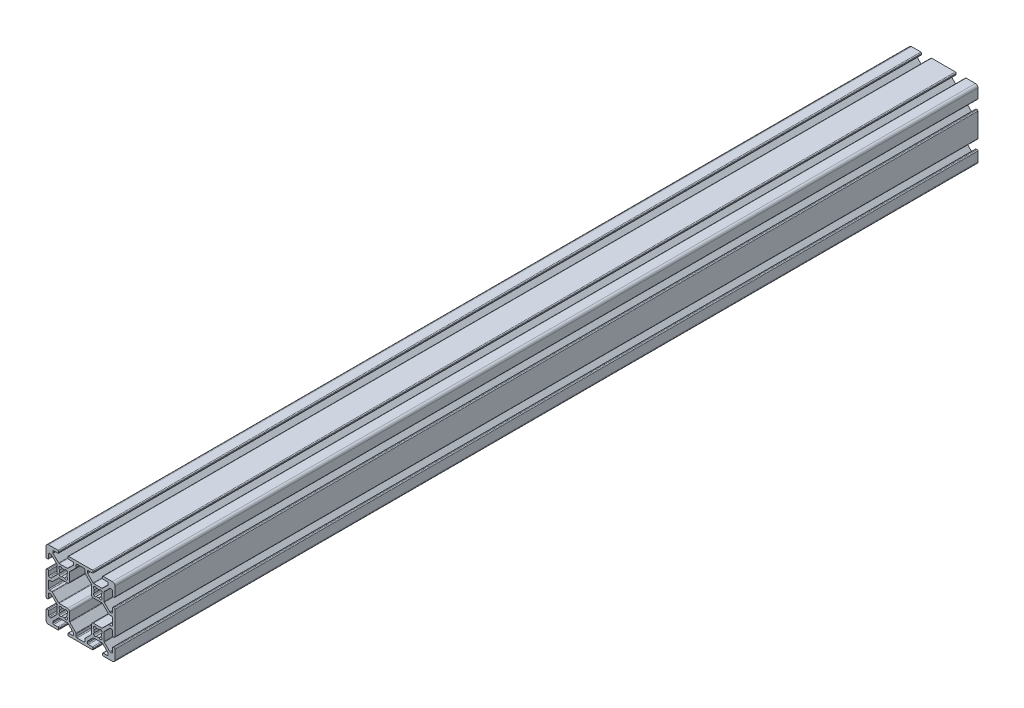
SolidWorks part; units mm, degrees
material "6105-T5 Aluminum"
ref_plane "Front Plane" through (0, 0, 0) normal (0, 0, 1) x (1, 0, 0)
ref_plane "Top Plane" through (0, 0, 0) normal (0, 1, 0) x (1, 0, 0)
ref_plane "Right Plane" through (0, 0, 0) normal (1, 0, 0) x (0, 0, -1)
sketch "Sketch1" plane through (0, 0, 0) normal (0, 0, 1) x (1, 0, 0)
  line L0 (-2.1249, 17.6955) -> (-2.3045, 17.8751)
  line L1 (-2.3045, 22.1249) -> (-2.1249, 22.3045)
  line L2 (2.1249, 22.3045) -> (2.3045, 22.1249)
  line L3 (2.3045, 17.8751) -> (2.1249, 17.6955)
  line L4 (-22.1249, 17.6955) -> (-22.3045, 17.8751)
  line L5 (-22.3045, 22.1249) -> (-22.1249, 22.3045)
  line L6 (-17.8751, 22.3045) -> (-17.6955, 22.1249)
  line L7 (-17.6955, 17.8751) -> (-17.8751, 17.6955)
  line L8 (-2.1249, -2.3045) -> (-2.3045, -2.1249)
  line L9 (-2.3045, 2.1249) -> (-2.1249, 2.3045)
  line L10 (2.1249, 2.3045) -> (2.3045, 2.1249)
  line L11 (2.3045, -2.1249) -> (2.1249, -2.3045)
  line L12 (-12.505, -7.992) -> (-12.505, -6.6448)
  line L13 (-12.6538, -6.2856) -> (-16.1962, -2.7431)
  line L14 (-16.345, -2.3839) -> (-16.345, 2.512)
  line L15 (-17.488, 3.655) -> (-22.3839, 3.655)
  line L16 (-22.7431, 3.8038) -> (-26.2856, 7.3462)
  line L17 (-26.6448, 7.495) -> (-27.992, 7.495)
  line L18 (-28.5, 8.003) -> (-28.5, 11.997)
  line L19 (-27.992, 12.505) -> (-26.6448, 12.505)
  line L20 (-26.2856, 12.6538) -> (-22.7431, 16.1962)
  line L21 (-22.3839, 16.345) -> (-17.488, 16.345)
  line L22 (-16.345, 17.488) -> (-16.345, 22.3839)
  line L23 (-16.1962, 22.7431) -> (-12.6538, 26.2856)
  line L24 (-12.505, 26.6448) -> (-12.505, 27.992)
  line L25 (-11.997, 28.5) -> (-8.003, 28.5)
  line L26 (-7.495, 27.992) -> (-7.495, 26.6448)
  line L27 (-7.3462, 26.2856) -> (-3.8038, 22.7431)
  line L28 (-3.655, 22.3839) -> (-3.655, 17.488)
  line L29 (-2.512, 16.345) -> (2.3839, 16.345)
  line L30 (2.7431, 16.1962) -> (6.2856, 12.6538)
  line L31 (6.6448, 12.505) -> (7.992, 12.505)
  line L32 (8.5, 11.997) -> (8.5, 8.003)
  line L33 (7.992, 7.495) -> (6.6448, 7.495)
  line L34 (6.2856, 7.3462) -> (2.7431, 3.8038)
  line L35 (2.3839, 3.655) -> (-2.512, 3.655)
  line L36 (-3.655, 2.512) -> (-3.655, -2.3839)
  line L37 (-3.8038, -2.7431) -> (-7.3462, -6.2856)
  line L38 (-7.495, -6.6448) -> (-7.495, -7.992)
  line L39 (-8.003, -8.5) -> (-11.997, -8.5)
  line L40 (-22.1249, -2.3045) -> (-22.3045, -2.1249)
  line L41 (-22.3045, 2.1249) -> (-22.1249, 2.3045)
  line L42 (-17.8751, 2.3045) -> (-17.6955, 2.1249)
  line L43 (-17.6955, -2.1249) -> (-17.8751, -2.3045)
  line L44 (-22.3839, -3.655) -> (-17.6161, -3.655)
  line L45 (-17.2569, -3.8038) -> (-14.1538, -6.9069)
  line L46 (-14.005, -7.2661) -> (-14.005, -7.992)
  line L47 (-14.513, -8.5) -> (-16.862, -8.5)
  line L48 (-17.37, -9.008) -> (-17.37, -9.492)
  line L49 (-16.862, -10) -> (-3.138, -10)
  line L50 (-2.63, -9.492) -> (-2.63, -9.008)
  line L51 (-3.138, -8.5) -> (-5.487, -8.5)
  line L52 (-5.995, -7.992) -> (-5.995, -7.2661)
  line L53 (-5.8462, -6.9069) -> (-2.7431, -3.8038)
  line L54 (-2.3839, -3.655) -> (2.3839, -3.655)
  line L55 (2.7431, -3.8038) -> (5.8462, -6.9069)
  line L56 (5.995, -7.2661) -> (5.995, -7.992)
  line L57 (5.487, -8.5) -> (3.138, -8.5)
  line L58 (2.63, -9.008) -> (2.63, -9.492)
  line L59 (3.138, -10) -> (8.5, -10)
  line L60 (10, -8.5) -> (10, -3.138)
  line L61 (9.492, -2.63) -> (9.008, -2.63)
  line L62 (8.5, -3.138) -> (8.5, -5.487)
  line L63 (7.992, -5.995) -> (7.2661, -5.995)
  line L64 (6.9069, -5.8462) -> (3.8038, -2.7431)
  line L65 (3.655, -2.3839) -> (3.655, 2.3839)
  line L66 (3.8038, 2.7431) -> (6.9069, 5.8462)
  line L67 (7.2661, 5.995) -> (7.992, 5.995)
  line L68 (8.5, 5.487) -> (8.5, 3.138)
  line L69 (9.008, 2.63) -> (9.492, 2.63)
  line L70 (10, 3.138) -> (10, 16.862)
  line L71 (9.492, 17.37) -> (9.008, 17.37)
  line L72 (8.5, 16.862) -> (8.5, 14.513)
  line L73 (7.992, 14.005) -> (7.2661, 14.005)
  line L74 (6.9069, 14.1538) -> (3.8038, 17.2569)
  line L75 (3.655, 17.6161) -> (3.655, 22.3839)
  line L76 (3.8038, 22.7431) -> (6.9069, 25.8462)
  line L77 (7.2661, 25.995) -> (7.992, 25.995)
  line L78 (8.5, 25.487) -> (8.5, 23.138)
  line L79 (9.008, 22.63) -> (9.492, 22.63)
  line L80 (10, 23.138) -> (10, 28.5)
  line L81 (8.5, 30) -> (3.138, 30)
  line L82 (2.63, 29.492) -> (2.63, 29.008)
  line L83 (3.138, 28.5) -> (5.487, 28.5)
  line L84 (5.995, 27.992) -> (5.995, 27.2661)
  line L85 (5.8462, 26.9069) -> (2.7431, 23.8038)
  line L86 (2.3839, 23.655) -> (-2.3839, 23.655)
  line L87 (-2.7431, 23.8038) -> (-5.8462, 26.9069)
  line L88 (-5.995, 27.2661) -> (-5.995, 27.992)
  line L89 (-5.487, 28.5) -> (-3.138, 28.5)
  line L90 (-2.63, 29.008) -> (-2.63, 29.492)
  line L91 (-3.138, 30) -> (-16.862, 30)
  line L92 (-17.37, 29.492) -> (-17.37, 29.008)
  line L93 (-16.862, 28.5) -> (-14.513, 28.5)
  line L94 (-14.005, 27.992) -> (-14.005, 27.2661)
  line L95 (-14.1538, 26.9069) -> (-17.2569, 23.8038)
  line L96 (-17.6161, 23.655) -> (-22.3839, 23.655)
  line L97 (-22.7431, 23.8038) -> (-25.8462, 26.9069)
  line L98 (-25.995, 27.2661) -> (-25.995, 27.992)
  line L99 (-25.487, 28.5) -> (-23.138, 28.5)
  line L100 (-22.63, 29.008) -> (-22.63, 29.492)
  line L101 (-23.138, 30) -> (-28.5, 30)
  line L102 (-30, 28.5) -> (-30, 23.138)
  line L103 (-29.492, 22.63) -> (-29.008, 22.63)
  line L104 (-28.5, 23.138) -> (-28.5, 25.487)
  line L105 (-27.992, 25.995) -> (-27.2661, 25.995)
  line L106 (-26.9069, 25.8462) -> (-23.8038, 22.7431)
  line L107 (-23.655, 22.3839) -> (-23.655, 17.6161)
  line L108 (-23.8038, 17.2569) -> (-26.9069, 14.1538)
  line L109 (-27.2661, 14.005) -> (-27.992, 14.005)
  line L110 (-28.5, 14.513) -> (-28.5, 16.862)
  line L111 (-29.008, 17.37) -> (-29.492, 17.37)
  line L112 (-30, 16.862) -> (-30, 3.138)
  line L113 (-29.492, 2.63) -> (-29.008, 2.63)
  line L114 (-28.5, 3.138) -> (-28.5, 5.487)
  line L115 (-27.992, 5.995) -> (-27.2661, 5.995)
  line L116 (-26.9069, 5.8462) -> (-23.8038, 2.7431)
  line L117 (-23.655, 2.3839) -> (-23.655, -2.3839)
  line L118 (-23.8038, -2.7431) -> (-26.9069, -5.8462)
  line L119 (-27.2661, -5.995) -> (-27.992, -5.995)
  line L120 (-28.5, -5.487) -> (-28.5, -3.138)
  line L121 (-29.008, -2.63) -> (-29.492, -2.63)
  line L122 (-30, -3.138) -> (-30, -8.5)
  line L123 (-28.5, -10) -> (-23.138, -10)
  line L124 (-22.63, -9.492) -> (-22.63, -9.008)
  line L125 (-23.138, -8.5) -> (-25.487, -8.5)
  line L126 (-25.995, -7.992) -> (-25.995, -7.2661)
  line L127 (-25.8462, -6.9069) -> (-22.7431, -3.8038)
  arc A0 (-1.9351, 19.196) -> (-2.3045, 17.8751) centre (-1.748, 18.4316) ccw
  arc A1 (-1.9351, 20.804) -> (-1.9351, 19.196) centre (0, 20) ccw
  arc A2 (-2.3045, 22.1249) -> (-1.9351, 20.804) centre (-1.748, 21.5684) ccw
  arc A3 (-0.804, 21.9351) -> (-2.1249, 22.3045) centre (-1.5684, 21.748) ccw
  arc A4 (0.804, 21.9351) -> (-0.804, 21.9351) centre (0, 20) ccw
  arc A5 (2.1249, 22.3045) -> (0.804, 21.9351) centre (1.5684, 21.748) ccw
  arc A6 (1.9351, 20.804) -> (2.3045, 22.1249) centre (1.748, 21.5684) ccw
  arc A7 (1.9351, 19.196) -> (1.9351, 20.804) centre (0, 20) ccw
  arc A8 (2.3045, 17.8751) -> (1.9351, 19.196) centre (1.748, 18.4316) ccw
  arc A9 (0.804, 18.0649) -> (2.1249, 17.6955) centre (1.5684, 18.252) ccw
  arc A10 (-0.804, 18.0649) -> (0.804, 18.0649) centre (0, 20) ccw
  arc A11 (-2.1249, 17.6955) -> (-0.804, 18.0649) centre (-1.5684, 18.252) ccw
  arc A12 (-21.9351, 19.196) -> (-22.3045, 17.8751) centre (-21.748, 18.4316) ccw
  arc A13 (-21.9351, 20.804) -> (-21.9351, 19.196) centre (-20, 20) ccw
  arc A14 (-22.3045, 22.1249) -> (-21.9351, 20.804) centre (-21.748, 21.5684) ccw
  arc A15 (-20.804, 21.9351) -> (-22.1249, 22.3045) centre (-21.5684, 21.748) ccw
  arc A16 (-19.196, 21.9351) -> (-20.804, 21.9351) centre (-20, 20) ccw
  arc A17 (-17.8751, 22.3045) -> (-19.196, 21.9351) centre (-18.4316, 21.748) ccw
  arc A18 (-18.0649, 20.804) -> (-17.6955, 22.1249) centre (-18.252, 21.5684) ccw
  arc A19 (-18.0649, 19.196) -> (-18.0649, 20.804) centre (-20, 20) ccw
  arc A20 (-17.6955, 17.8751) -> (-18.0649, 19.196) centre (-18.252, 18.4316) ccw
  arc A21 (-19.196, 18.0649) -> (-17.8751, 17.6955) centre (-18.4316, 18.252) ccw
  arc A22 (-20.804, 18.0649) -> (-19.196, 18.0649) centre (-20, 20) ccw
  arc A23 (-22.1249, 17.6955) -> (-20.804, 18.0649) centre (-21.5684, 18.252) ccw
  arc A24 (-1.9351, -0.804) -> (-2.3045, -2.1249) centre (-1.748, -1.5684) ccw
  arc A25 (-1.9351, 0.804) -> (-1.9351, -0.804) centre (0, 0) ccw
  arc A26 (-2.3045, 2.1249) -> (-1.9351, 0.804) centre (-1.748, 1.5684) ccw
  arc A27 (-0.804, 1.9351) -> (-2.1249, 2.3045) centre (-1.5684, 1.748) ccw
  arc A28 (0.804, 1.9351) -> (-0.804, 1.9351) centre (0, 0) ccw
  arc A29 (2.1249, 2.3045) -> (0.804, 1.9351) centre (1.5684, 1.748) ccw
  arc A30 (1.9351, 0.804) -> (2.3045, 2.1249) centre (1.748, 1.5684) ccw
  arc A31 (1.9351, -0.804) -> (1.9351, 0.804) centre (0, 0) ccw
  arc A32 (2.3045, -2.1249) -> (1.9351, -0.804) centre (1.748, -1.5684) ccw
  arc A33 (0.804, -1.9351) -> (2.1249, -2.3045) centre (1.5684, -1.748) ccw
  arc A34 (-0.804, -1.9351) -> (0.804, -1.9351) centre (0, 0) ccw
  arc A35 (-2.1249, -2.3045) -> (-0.804, -1.9351) centre (-1.5684, -1.748) ccw
  arc A36 (-12.505, -7.992) -> (-11.997, -8.5) centre (-11.997, -7.992) ccw
  arc A37 (-12.505, -6.6448) -> (-12.6538, -6.2856) centre (-13.013, -6.6448) ccw
  arc A38 (-16.345, -2.3839) -> (-16.1962, -2.7431) centre (-15.837, -2.3839) ccw
  arc A39 (-16.345, 2.512) -> (-17.488, 3.655) centre (-17.488, 2.512) ccw
  arc A40 (-22.7431, 3.8038) -> (-22.3839, 3.655) centre (-22.3839, 4.163) ccw
  arc A41 (-26.2856, 7.3462) -> (-26.6448, 7.495) centre (-26.6448, 6.987) ccw
  arc A42 (-28.5, 8.003) -> (-27.992, 7.495) centre (-27.992, 8.003) ccw
  arc A43 (-27.992, 12.505) -> (-28.5, 11.997) centre (-27.992, 11.997) ccw
  arc A44 (-26.6448, 12.505) -> (-26.2856, 12.6538) centre (-26.6448, 13.013) ccw
  arc A45 (-22.3839, 16.345) -> (-22.7431, 16.1962) centre (-22.3839, 15.837) ccw
  arc A46 (-17.488, 16.345) -> (-16.345, 17.488) centre (-17.488, 17.488) ccw
  arc A47 (-16.1962, 22.7431) -> (-16.345, 22.3839) centre (-15.837, 22.3839) ccw
  arc A48 (-12.6538, 26.2856) -> (-12.505, 26.6448) centre (-13.013, 26.6448) ccw
  arc A49 (-11.997, 28.5) -> (-12.505, 27.992) centre (-11.997, 27.992) ccw
  arc A50 (-7.495, 27.992) -> (-8.003, 28.5) centre (-8.003, 27.992) ccw
  arc A51 (-7.495, 26.6448) -> (-7.3462, 26.2856) centre (-6.987, 26.6448) ccw
  arc A52 (-3.655, 22.3839) -> (-3.8038, 22.7431) centre (-4.163, 22.3839) ccw
  arc A53 (-3.655, 17.488) -> (-2.512, 16.345) centre (-2.512, 17.488) ccw
  arc A54 (2.7431, 16.1962) -> (2.3839, 16.345) centre (2.3839, 15.837) ccw
  arc A55 (6.2856, 12.6538) -> (6.6448, 12.505) centre (6.6448, 13.013) ccw
  arc A56 (8.5, 11.997) -> (7.992, 12.505) centre (7.992, 11.997) ccw
  arc A57 (7.992, 7.495) -> (8.5, 8.003) centre (7.992, 8.003) ccw
  arc A58 (6.6448, 7.495) -> (6.2856, 7.3462) centre (6.6448, 6.987) ccw
  arc A59 (2.3839, 3.655) -> (2.7431, 3.8038) centre (2.3839, 4.163) ccw
  arc A60 (-2.512, 3.655) -> (-3.655, 2.512) centre (-2.512, 2.512) ccw
  arc A61 (-3.8038, -2.7431) -> (-3.655, -2.3839) centre (-4.163, -2.3839) ccw
  arc A62 (-7.3462, -6.2856) -> (-7.495, -6.6448) centre (-6.987, -6.6448) ccw
  arc A63 (-8.003, -8.5) -> (-7.495, -7.992) centre (-8.003, -7.992) ccw
  arc A64 (-21.9351, -0.804) -> (-22.3045, -2.1249) centre (-21.748, -1.5684) ccw
  arc A65 (-21.9351, 0.804) -> (-21.9351, -0.804) centre (-20, 0) ccw
  arc A66 (-22.3045, 2.1249) -> (-21.9351, 0.804) centre (-21.748, 1.5684) ccw
  arc A67 (-20.804, 1.9351) -> (-22.1249, 2.3045) centre (-21.5684, 1.748) ccw
  arc A68 (-19.196, 1.9351) -> (-20.804, 1.9351) centre (-20, 0) ccw
  arc A69 (-17.8751, 2.3045) -> (-19.196, 1.9351) centre (-18.4316, 1.748) ccw
  arc A70 (-18.0649, 0.804) -> (-17.6955, 2.1249) centre (-18.252, 1.5684) ccw
  arc A71 (-18.0649, -0.804) -> (-18.0649, 0.804) centre (-20, 0) ccw
  arc A72 (-17.6955, -2.1249) -> (-18.0649, -0.804) centre (-18.252, -1.5684) ccw
  arc A73 (-19.196, -1.9351) -> (-17.8751, -2.3045) centre (-18.4316, -1.748) ccw
  arc A74 (-20.804, -1.9351) -> (-19.196, -1.9351) centre (-20, 0) ccw
  arc A75 (-22.1249, -2.3045) -> (-20.804, -1.9351) centre (-21.5684, -1.748) ccw
  arc A76 (-22.3839, -3.655) -> (-22.7431, -3.8038) centre (-22.3839, -4.163) ccw
  arc A77 (-17.2569, -3.8038) -> (-17.6161, -3.655) centre (-17.6161, -4.163) ccw
  arc A78 (-14.005, -7.2661) -> (-14.1538, -6.9069) centre (-14.513, -7.2661) ccw
  arc A79 (-14.513, -8.5) -> (-14.005, -7.992) centre (-14.513, -7.992) ccw
  arc A80 (-16.862, -8.5) -> (-17.37, -9.008) centre (-16.862, -9.008) ccw
  arc A81 (-17.37, -9.492) -> (-16.862, -10) centre (-16.862, -9.492) ccw
  arc A82 (-3.138, -10) -> (-2.63, -9.492) centre (-3.138, -9.492) ccw
  arc A83 (-2.63, -9.008) -> (-3.138, -8.5) centre (-3.138, -9.008) ccw
  arc A84 (-5.995, -7.992) -> (-5.487, -8.5) centre (-5.487, -7.992) ccw
  arc A85 (-5.8462, -6.9069) -> (-5.995, -7.2661) centre (-5.487, -7.2661) ccw
  arc A86 (-2.3839, -3.655) -> (-2.7431, -3.8038) centre (-2.3839, -4.163) ccw
  arc A87 (2.7431, -3.8038) -> (2.3839, -3.655) centre (2.3839, -4.163) ccw
  arc A88 (5.995, -7.2661) -> (5.8462, -6.9069) centre (5.487, -7.2661) ccw
  arc A89 (5.487, -8.5) -> (5.995, -7.992) centre (5.487, -7.992) ccw
  arc A90 (3.138, -8.5) -> (2.63, -9.008) centre (3.138, -9.008) ccw
  arc A91 (2.63, -9.492) -> (3.138, -10) centre (3.138, -9.492) ccw
  arc A92 (8.5, -10) -> (10, -8.5) centre (8.5, -8.5) ccw
  arc A93 (10, -3.138) -> (9.492, -2.63) centre (9.492, -3.138) ccw
  arc A94 (9.008, -2.63) -> (8.5, -3.138) centre (9.008, -3.138) ccw
  arc A95 (7.992, -5.995) -> (8.5, -5.487) centre (7.992, -5.487) ccw
  arc A96 (6.9069, -5.8462) -> (7.2661, -5.995) centre (7.2661, -5.487) ccw
  arc A97 (3.655, -2.3839) -> (3.8038, -2.7431) centre (4.163, -2.3839) ccw
  arc A98 (3.8038, 2.7431) -> (3.655, 2.3839) centre (4.163, 2.3839) ccw
  arc A99 (7.2661, 5.995) -> (6.9069, 5.8462) centre (7.2661, 5.487) ccw
  arc A100 (8.5, 5.487) -> (7.992, 5.995) centre (7.992, 5.487) ccw
  arc A101 (8.5, 3.138) -> (9.008, 2.63) centre (9.008, 3.138) ccw
  arc A102 (9.492, 2.63) -> (10, 3.138) centre (9.492, 3.138) ccw
  arc A103 (10, 16.862) -> (9.492, 17.37) centre (9.492, 16.862) ccw
  arc A104 (9.008, 17.37) -> (8.5, 16.862) centre (9.008, 16.862) ccw
  arc A105 (7.992, 14.005) -> (8.5, 14.513) centre (7.992, 14.513) ccw
  arc A106 (6.9069, 14.1538) -> (7.2661, 14.005) centre (7.2661, 14.513) ccw
  arc A107 (3.655, 17.6161) -> (3.8038, 17.2569) centre (4.163, 17.6161) ccw
  arc A108 (3.8038, 22.7431) -> (3.655, 22.3839) centre (4.163, 22.3839) ccw
  arc A109 (7.2661, 25.995) -> (6.9069, 25.8462) centre (7.2661, 25.487) ccw
  arc A110 (8.5, 25.487) -> (7.992, 25.995) centre (7.992, 25.487) ccw
  arc A111 (8.5, 23.138) -> (9.008, 22.63) centre (9.008, 23.138) ccw
  arc A112 (9.492, 22.63) -> (10, 23.138) centre (9.492, 23.138) ccw
  arc A113 (10, 28.5) -> (8.5, 30) centre (8.5, 28.5) ccw
  arc A114 (3.138, 30) -> (2.63, 29.492) centre (3.138, 29.492) ccw
  arc A115 (2.63, 29.008) -> (3.138, 28.5) centre (3.138, 29.008) ccw
  arc A116 (5.995, 27.992) -> (5.487, 28.5) centre (5.487, 27.992) ccw
  arc A117 (5.8462, 26.9069) -> (5.995, 27.2661) centre (5.487, 27.2661) ccw
  arc A118 (2.3839, 23.655) -> (2.7431, 23.8038) centre (2.3839, 24.163) ccw
  arc A119 (-2.7431, 23.8038) -> (-2.3839, 23.655) centre (-2.3839, 24.163) ccw
  arc A120 (-5.995, 27.2661) -> (-5.8462, 26.9069) centre (-5.487, 27.2661) ccw
  arc A121 (-5.487, 28.5) -> (-5.995, 27.992) centre (-5.487, 27.992) ccw
  arc A122 (-3.138, 28.5) -> (-2.63, 29.008) centre (-3.138, 29.008) ccw
  arc A123 (-2.63, 29.492) -> (-3.138, 30) centre (-3.138, 29.492) ccw
  arc A124 (-16.862, 30) -> (-17.37, 29.492) centre (-16.862, 29.492) ccw
  arc A125 (-17.37, 29.008) -> (-16.862, 28.5) centre (-16.862, 29.008) ccw
  arc A126 (-14.005, 27.992) -> (-14.513, 28.5) centre (-14.513, 27.992) ccw
  arc A127 (-14.1538, 26.9069) -> (-14.005, 27.2661) centre (-14.513, 27.2661) ccw
  arc A128 (-17.6161, 23.655) -> (-17.2569, 23.8038) centre (-17.6161, 24.163) ccw
  arc A129 (-22.7431, 23.8038) -> (-22.3839, 23.655) centre (-22.3839, 24.163) ccw
  arc A130 (-25.995, 27.2661) -> (-25.8462, 26.9069) centre (-25.487, 27.2661) ccw
  arc A131 (-25.487, 28.5) -> (-25.995, 27.992) centre (-25.487, 27.992) ccw
  arc A132 (-23.138, 28.5) -> (-22.63, 29.008) centre (-23.138, 29.008) ccw
  arc A133 (-22.63, 29.492) -> (-23.138, 30) centre (-23.138, 29.492) ccw
  arc A134 (-28.5, 30) -> (-30, 28.5) centre (-28.5, 28.5) ccw
  arc A135 (-30, 23.138) -> (-29.492, 22.63) centre (-29.492, 23.138) ccw
  arc A136 (-29.008, 22.63) -> (-28.5, 23.138) centre (-29.008, 23.138) ccw
  arc A137 (-27.992, 25.995) -> (-28.5, 25.487) centre (-27.992, 25.487) ccw
  arc A138 (-26.9069, 25.8462) -> (-27.2661, 25.995) centre (-27.2661, 25.487) ccw
  arc A139 (-23.655, 22.3839) -> (-23.8038, 22.7431) centre (-24.163, 22.3839) ccw
  arc A140 (-23.8038, 17.2569) -> (-23.655, 17.6161) centre (-24.163, 17.6161) ccw
  arc A141 (-27.2661, 14.005) -> (-26.9069, 14.1538) centre (-27.2661, 14.513) ccw
  arc A142 (-28.5, 14.513) -> (-27.992, 14.005) centre (-27.992, 14.513) ccw
  arc A143 (-28.5, 16.862) -> (-29.008, 17.37) centre (-29.008, 16.862) ccw
  arc A144 (-29.492, 17.37) -> (-30, 16.862) centre (-29.492, 16.862) ccw
  arc A145 (-30, 3.138) -> (-29.492, 2.63) centre (-29.492, 3.138) ccw
  arc A146 (-29.008, 2.63) -> (-28.5, 3.138) centre (-29.008, 3.138) ccw
  arc A147 (-27.992, 5.995) -> (-28.5, 5.487) centre (-27.992, 5.487) ccw
  arc A148 (-26.9069, 5.8462) -> (-27.2661, 5.995) centre (-27.2661, 5.487) ccw
  arc A149 (-23.655, 2.3839) -> (-23.8038, 2.7431) centre (-24.163, 2.3839) ccw
  arc A150 (-23.8038, -2.7431) -> (-23.655, -2.3839) centre (-24.163, -2.3839) ccw
  arc A151 (-27.2661, -5.995) -> (-26.9069, -5.8462) centre (-27.2661, -5.487) ccw
  arc A152 (-28.5, -5.487) -> (-27.992, -5.995) centre (-27.992, -5.487) ccw
  arc A153 (-28.5, -3.138) -> (-29.008, -2.63) centre (-29.008, -3.138) ccw
  arc A154 (-29.492, -2.63) -> (-30, -3.138) centre (-29.492, -3.138) ccw
  arc A155 (-30, -8.5) -> (-28.5, -10) centre (-28.5, -8.5) ccw
  arc A156 (-23.138, -10) -> (-22.63, -9.492) centre (-23.138, -9.492) ccw
  arc A157 (-22.63, -9.008) -> (-23.138, -8.5) centre (-23.138, -9.008) ccw
  arc A158 (-25.995, -7.992) -> (-25.487, -8.5) centre (-25.487, -7.992) ccw
  arc A159 (-25.8462, -6.9069) -> (-25.995, -7.2661) centre (-25.487, -7.2661) ccw
extrude "Extrude1" add sketch "Sketch1" against normal blind 500
